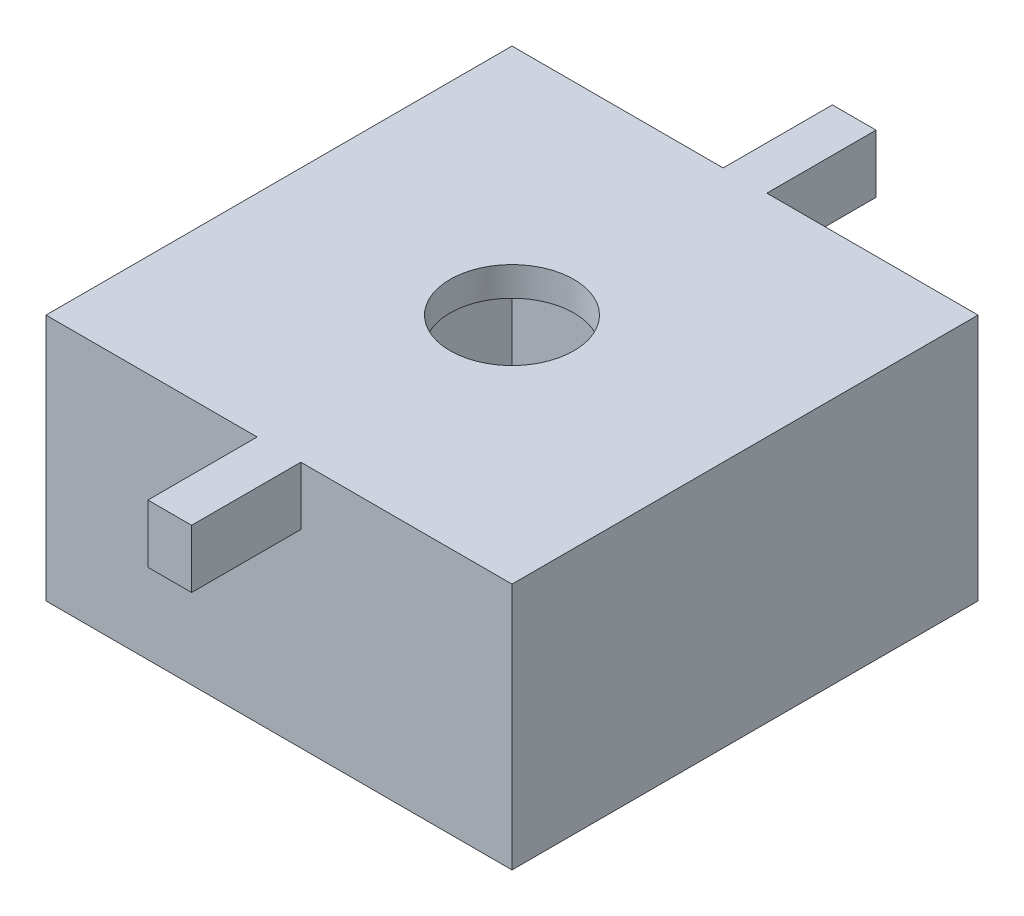
SolidWorks part; units mm, degrees
ref_plane "Front Plane" through (0, 0, 0) normal (0, 0, 1) x (1, 0, 0)
ref_plane "Top Plane" through (0, 0, 0) normal (0, 1, 0) x (1, 0, 0)
ref_plane "Right Plane" through (0, 0, 0) normal (1, 0, 0) x (0, 0, -1)
sketch "Sketch1" plane through (0, 0, 0) normal (0, 1, 0) x (1, 0, 0)
  line L0 (16, 16) -> (-16, 16)
  line L1 (14, -14) -> (-14, -14)
  line L2 (14, -14) -> (14, 14)
  line L3 (14, 14) -> (-14, 14)
  line L4 (-14, -14) -> (-14, 14)
  line L5 (14, -14) -> (-14, 14) construction
  line L6 (14, 14) -> (-14, -14) construction
  line L7 (-16, -16) -> (-16, 16)
  line L8 (16, -16) -> (-16, -16)
  line L9 (16, -16) -> (16, 16)
  point P0 (0, 0)
  dimension "D1" = 28
  dimension "D2" = 2
extrude "Boss-Extrude1" add sketch "Sketch1" along normal blind 15
sketch "Sketch2" plane through (0, 15, 0) normal (0, 1, 0) x (1, 0, 0)
  line L1 (-16, -16) -> (16, -16)
  line L2 (-16, -16) -> (-16, 16)
  line L3 (-16, 16) -> (16, 16)
  line L4 (16, -16) -> (16, 16)
  line L5 (-16, -16) -> (16, 16) construction
  line L6 (-16, 16) -> (16, -16) construction
  point P0 (0, 0)
extrude "Boss-Extrude2" add sketch "Sketch2" along normal blind 2
sketch "Sketch3" plane through (0, 17, 0) normal (0, 1, 0) x (1, 0, 0)
  circle A0 centre (0, 0) radius 4.25
  dimension "D1" = 8.5
extrude "Cut-Extrude1" cut sketch "Sketch3" against normal up to next
sketch "Sketch5" plane through (0, 0, -16) normal (0, 0, -1) x (-1, 0, 0)
  line L0 (0, 0) -> (0, 17) construction
  line L1 (-16, 0) -> (16, 0) construction
  line L2 (-16, 17) -> (16, 17) construction
  line L3 (-16, 8.5) -> (16, 8.5) construction
  line L4 (-16, 17) -> (-16, 0) construction
  line L5 (16, 17) -> (16, 0) construction
  line L7 (1.5, 13) -> (-1.5, 13)
  line L8 (1.5, 13) -> (1.5, 17)
  line L9 (1.5, 17) -> (-1.5, 17)
  line L10 (-1.5, 13) -> (-1.5, 17)
  line L11 (1.5, 13) -> (-1.5, 17) construction
  line L12 (1.5, 17) -> (-1.5, 13) construction
  point P12 (0, 15)
  dimension "D1" = 3
  dimension "D2" = 4
extrude "Boss-Extrude3" add sketch "Sketch5" along normal blind 7.5
mirror "Mirror1" about plane through (0, 0, 0) normal (0, 0, 1) of "Boss-Extrude3"
